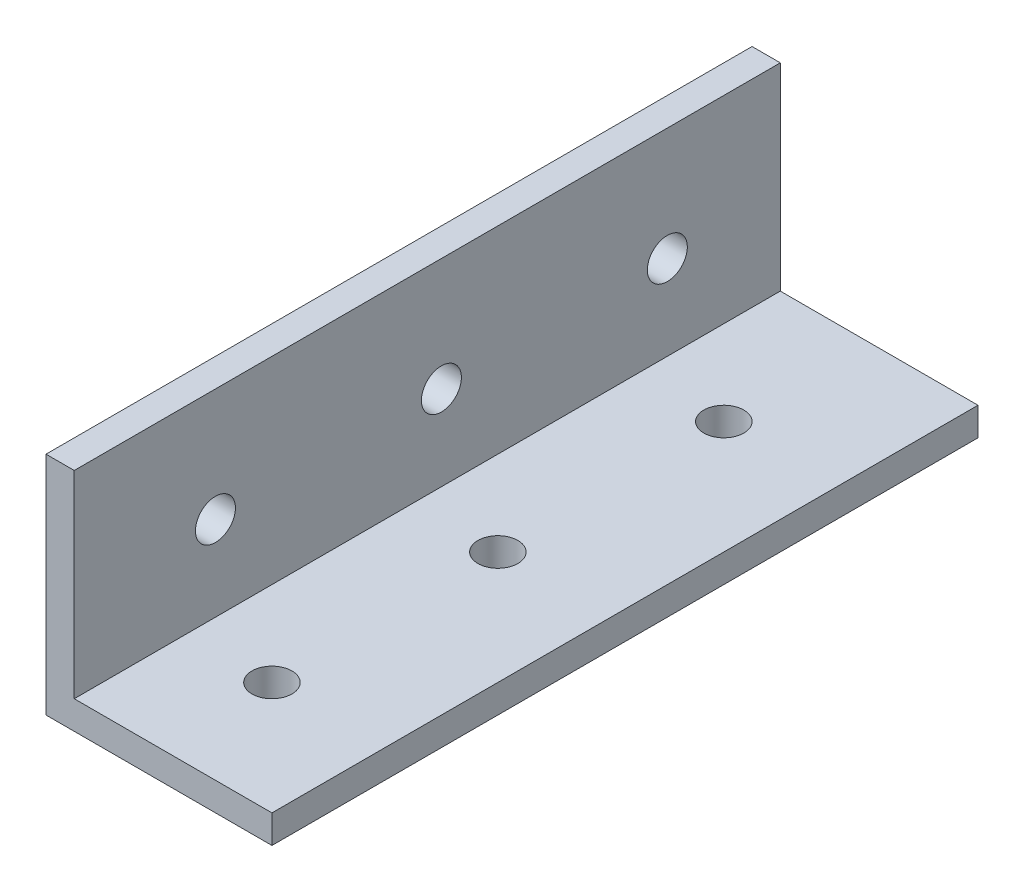
SolidWorks part; units mm, degrees
material "6061-T6 (SS)"
ref_plane "Front Plane" through (0, 0, 0) normal (0, 0, 1) x (1, 0, 0)
ref_plane "Top Plane" through (0, 0, 0) normal (0, 1, 0) x (1, 0, 0)
ref_plane "Right Plane" through (0, 0, 0) normal (1, 0, 0) x (0, 0, -1)
sketch "Sketch1" plane through (0, 0, 0) normal (0, 0, 1) x (1, 0, 0)
  line L1 (0, 0) -> (25.4, 0)
  line L2 (0, 0) -> (0, 25.4)
  line L3 (0, 25.4) -> (3.175, 25.4)
  line L4 (25.4, 0) -> (25.4, 3.175)
  line L7 (25.4, 3.175) -> (3.175, 3.175)
  line L8 (3.175, 25.4) -> (3.175, 3.175)
  dimension "D1" = 25.4
  dimension "D2" = 25.4
  dimension "D3" = 3.175
  dimension "D4" = 3.175
extrude "Boss-Extrude1" add sketch "Sketch1" along normal blind 79.375
hole_wizard "#8 Clearance Hole1" positions "Sketch3" profile "Sketch2" hole size "#8" standard "ANSI Inch" end condition through all
sketch "Sketch3" plane through (0, 0, 0) normal (0, -1, 0) x (1, 0, 0)
  line L0 (0, 79.375) -> (25.4, 79.375) construction
  line L1 (25.4, 79.375) -> (25.4, 0) construction
  point P0 (12.7, 66.675)
  point P2 (12.7, 41.275)
  point P4 (12.7, 15.875)
  dimension "D1" = 25.4
  dimension "D2" = 25.4
  dimension "D3" = 12.7
  dimension "D4" = 12.7
sketch "Sketch2" plane through (12.7, 0, 66.675) normal (1, 0, 0) x (0, 0, -1)
  line L0 (0, 0) -> (0, 25.4)
  line L1 (0, 25.4) -> (2.2479, 25.4)
  line L2 (2.2479, 25.4) -> (2.2479, 0)
  line L5 (2.2479, 0) -> (0, 0)
  line L11 (0, -6.35) -> (0, 107.95) construction
  dimension "Thru Hole Dia." = 4.4958
  dimension "Thru Hole Depth" = 25.4
hole_wizard "#8 Clearance Hole2" positions "Sketch5" profile "Sketch4" hole size "#8" standard "ANSI Inch" end condition through all
sketch "Sketch5" plane through (0, 0, 0) normal (-1, 0, 0) x (0, 0, 1)
  line L0 (0, 25.4) -> (0, 0) construction
  line L1 (79.375, 0) -> (0, 0) construction
  point P0 (63.5, 12.7)
  point P2 (38.1, 12.7)
  point P4 (12.7, 12.7)
  dimension "D1" = 25.4
  dimension "D2" = 25.4
  dimension "D3" = 12.7
  dimension "D4" = 12.7
sketch "Sketch4" plane through (0, 12.7, 63.5) normal (0, 1, 0) x (0, 0, 1)
  line L0 (0, 0) -> (0, 25.4)
  line L1 (0, 25.4) -> (2.2479, 25.4)
  line L2 (2.2479, 25.4) -> (2.2479, 0)
  line L5 (2.2479, 0) -> (0, 0)
  line L11 (0, -6.35) -> (0, 107.95) construction
  dimension "Thru Hole Dia." = 4.4958
  dimension "Thru Hole Depth" = 25.4
